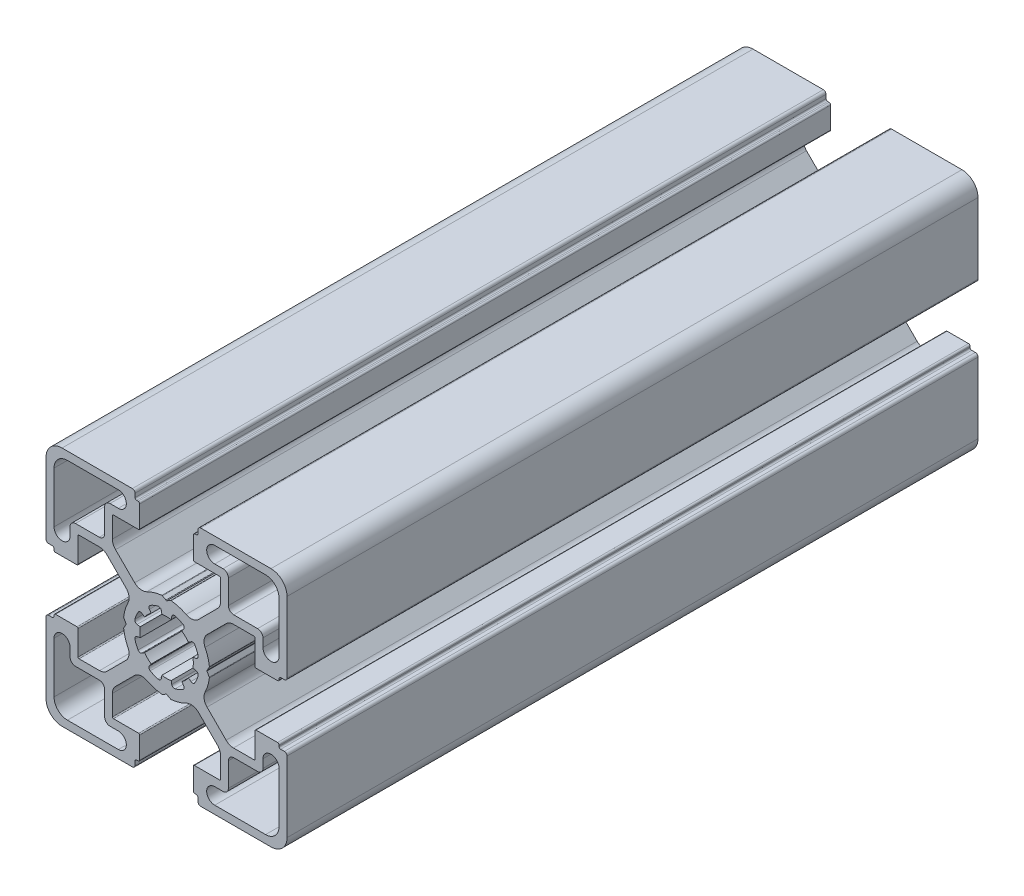
SolidWorks part; units mm, degrees
ref_plane "Front Plane" through (0, 0, 0) normal (0, 0, 1) x (1, 0, 0)
ref_plane "Top Plane" through (0, 0, 0) normal (0, 1, 0) x (1, 0, 0)
ref_plane "Right Plane" through (0, 0, 0) normal (1, 0, 0) x (0, 0, -1)
sketch "Sketch1" plane through (0, 0, 0) normal (0, 0, 1) x (1, 0, 0)
  line L0 (10.55, 18) -> (9, 18)
  line L1 (18.5, 21) -> (9, 21)
  line L2 (21, 9.0002) -> (21, 18.5)
  line L3 (18, 9.0002) -> (18, 10.55)
  line L4 (17, 11.55) -> (12.55, 11.55)
  line L5 (11.55, 12.55) -> (11.55, 17)
  line L6 (7.974, 0.7926) -> (7.5401, 0.0468)
  line L7 (-0.8674, 4.9242) -> (-0.9675, 5.4811)
  line L8 (-3.1913, 4.5626) -> (-2.864, 4.0985)
  line L9 (-4.0897, 2.8765) -> (-4.5668, 3.2082)
  line L10 (-5.4897, 0.9862) -> (-4.9205, 0.8878)
  line L11 (11.1298, 9.425) -> (7.5635, 5.8587)
  line L12 (16.3169, 9.9945) -> (12.5048, 9.9945)
  line L13 (16.5169, 5.2) -> (16.5169, 9.7945)
  line L14 (20.7196, 5) -> (16.7169, 5)
  line L15 (21.0196, 5.3) -> (21.0196, 5.5)
  line L16 (22, 5.8) -> (21.3196, 5.8)
  line L17 (22.5, 6.3) -> (22.5, 19.5)
  line L18 (19.5, 22.5) -> (6.3757, 22.5)
  line L19 (5.8757, 21.3) -> (5.8757, 22)
  line L20 (5.5757, 21) -> (5.3, 21)
  line L21 (5, 16.6668) -> (5, 20.7)
  line L22 (9.9054, 16.4668) -> (5.2, 16.4668)
  line L23 (10.1054, 12.4716) -> (10.1054, 16.2668)
  line L24 (5.9449, 7.4827) -> (9.5196, 11.0574)
  line L25 (0.1126, 7.6069) -> (0.7547, 7.9748)
  line L26 (5.4897, 0.9862) -> (4.9205, 0.8878)
  line L27 (4.0897, 2.8765) -> (4.5668, 3.2082)
  line L28 (3.1913, 4.5626) -> (2.864, 4.0985)
  line L29 (0.8674, 4.9242) -> (0.9675, 5.4811)
  line L30 (-10.55, -18) -> (-9, -18)
  line L31 (-18.5, -21) -> (-9, -21)
  line L32 (-21, -9.0002) -> (-21, -18.5)
  line L33 (-18, -9.0002) -> (-18, -10.55)
  line L34 (-17, -11.55) -> (-12.55, -11.55)
  line L35 (-11.55, -12.55) -> (-11.55, -17)
  line L36 (-7.974, -0.7926) -> (-7.5401, -0.0468)
  line L37 (-11.1298, -9.425) -> (-7.5635, -5.8587)
  line L38 (-16.3169, -9.9945) -> (-12.5048, -9.9945)
  line L39 (-16.5169, -5.2) -> (-16.5169, -9.7945)
  line L40 (-20.7196, -5) -> (-16.7169, -5)
  line L41 (-21.0196, -5.3) -> (-21.0196, -5.5)
  line L42 (-22, -5.8) -> (-21.3196, -5.8)
  line L43 (-22.5, -6.3) -> (-22.5, -19.5)
  line L44 (-19.5, -22.5) -> (-6.3757, -22.5)
  line L45 (-5.8757, -21.3) -> (-5.8757, -22)
  line L46 (-5.5757, -21) -> (-5.3, -21)
  line L47 (-5, -16.6668) -> (-5, -20.7)
  line L48 (-9.9054, -16.4668) -> (-5.2, -16.4668)
  line L49 (-10.1054, -12.4716) -> (-10.1054, -16.2668)
  line L50 (-5.9449, -7.4827) -> (-9.5196, -11.0574)
  line L51 (-0.1126, -7.6069) -> (-0.7547, -7.9748)
  line L52 (0.8674, -4.9242) -> (0.9675, -5.4811)
  line L53 (3.1913, -4.5626) -> (2.864, -4.0985)
  line L54 (4.0897, -2.8765) -> (4.5668, -3.2082)
  line L55 (5.4897, -0.9862) -> (4.9205, -0.8878)
  line L56 (0.1126, -7.6069) -> (0.7547, -7.9748)
  line L57 (5.9449, -7.4827) -> (9.5196, -11.0574)
  line L58 (10.1054, -12.4716) -> (10.1054, -16.2668)
  line L59 (9.9054, -16.4668) -> (5.2, -16.4668)
  line L60 (5, -16.6668) -> (5, -20.7)
  line L61 (5.5757, -21) -> (5.3, -21)
  line L62 (-0.1126, 7.6069) -> (-0.7547, 7.9748)
  line L63 (-5.9449, 7.4827) -> (-9.5196, 11.0574)
  line L64 (-10.1054, 12.4716) -> (-10.1054, 16.2668)
  line L65 (-9.9054, 16.4668) -> (-5.2, 16.4668)
  line L66 (-5, 16.6668) -> (-5, 20.7)
  line L67 (-5.5757, 21) -> (-5.3, 21)
  line L68 (-5.8757, 21.3) -> (-5.8757, 22)
  line L69 (-19.5, 22.5) -> (-6.3757, 22.5)
  line L70 (-22.5, 6.3) -> (-22.5, 19.5)
  line L71 (-22, 5.8) -> (-21.3196, 5.8)
  line L72 (-21.0196, 5.3) -> (-21.0196, 5.5)
  line L73 (-20.7196, 5) -> (-16.7169, 5)
  line L74 (-16.5169, 5.2) -> (-16.5169, 9.7945)
  line L75 (-16.3169, 9.9945) -> (-12.5048, 9.9945)
  line L76 (-11.1298, 9.425) -> (-7.5635, 5.8587)
  line L77 (-7.974, 0.7926) -> (-7.5401, 0.0468)
  line L78 (5.8757, -21.3) -> (5.8757, -22)
  line L79 (19.5, -22.5) -> (6.3757, -22.5)
  line L80 (22.5, -6.3) -> (22.5, -19.5)
  line L81 (22, -5.8) -> (21.3196, -5.8)
  line L82 (21.0196, -5.3) -> (21.0196, -5.5)
  line L83 (20.7196, -5) -> (16.7169, -5)
  line L84 (16.5169, -5.2) -> (16.5169, -9.7945)
  line L85 (16.3169, -9.9945) -> (12.5048, -9.9945)
  line L86 (11.1298, -9.425) -> (7.5635, -5.8587)
  line L87 (-5.4897, -0.9862) -> (-4.9205, -0.8878)
  line L88 (-4.0897, -2.8765) -> (-4.5668, -3.2082)
  line L89 (-3.1913, -4.5626) -> (-2.864, -4.0985)
  line L90 (-0.8674, -4.9242) -> (-0.9675, -5.4811)
  line L91 (7.974, -0.7926) -> (7.5401, -0.0468)
  line L92 (-11.55, 12.55) -> (-11.55, 17)
  line L93 (-17, 11.55) -> (-12.55, 11.55)
  line L94 (-18, 9.0002) -> (-18, 10.55)
  line L95 (-21, 9.0002) -> (-21, 18.5)
  line L96 (-18.5, 21) -> (-9, 21)
  line L97 (-10.55, 18) -> (-9, 18)
  line L98 (11.55, -12.55) -> (11.55, -17)
  line L99 (17, -11.55) -> (12.55, -11.55)
  line L100 (18, -9.0002) -> (18, -10.55)
  line L101 (21, -9.0002) -> (21, -18.5)
  line L102 (18.5, -21) -> (9, -21)
  line L103 (10.55, -18) -> (9, -18)
  line L104 (-33.3633, 0) -> (37.7265, 0) construction
  line L105 (0, 32.2957) -> (0, -36.0465) construction
  arc A0 (9, 18) -> (9, 21) centre (9, 19.5) cw
  arc A1 (18.5, 21) -> (21, 18.5) centre (18.5, 18.5) cw
  arc A2 (21, 9.0002) -> (18, 9.0002) centre (19.5, 9.0002) cw
  arc A3 (17, 11.55) -> (18, 10.55) centre (17, 10.55) cw
  arc A4 (12.55, 11.55) -> (11.55, 12.55) centre (12.55, 12.55) cw
  arc A5 (10.55, 18) -> (11.55, 17) centre (10.55, 17) cw
  arc A6 (7.5313, 0) -> (7.5401, 0.0468) centre (7.7309, -0.013) cw
  arc A7 (8, 0.9141) -> (7.974, 0.7926) centre (7.8011, 0.8932) cw
  arc A8 (7.2004, 3.6119) -> (8, 0.9141) centre (0.0496, 0.0249) cw
  arc A9 (7.2004, 3.6119) -> (7.5635, 5.8587) centre (8.9385, 4.4837) cw
  arc A10 (11.1298, 9.425) -> (12.5048, 9.9945) centre (12.5048, 8.05) cw
  arc A11 (16.3169, 9.9945) -> (16.5169, 9.7945) centre (16.3169, 9.7945) cw
  arc A12 (16.7169, 5) -> (16.5169, 5.2) centre (16.7169, 5.2) cw
  arc A13 (21.0196, 5.3) -> (20.7196, 5) centre (20.7196, 5.3) cw
  arc A14 (0.8674, 4.9242) -> (-0.8674, 4.9242) centre (0, 0) ccw
  arc A15 (-0.9675, 5.4811) -> (-1.5951, 5.8941) centre (-1.4627, 5.4119) ccw
  arc A16 (-1.5951, 5.8941) -> (-3.0444, 5.2994) centre (-0.0235, 0) ccw
  arc A17 (-3.0444, 5.2994) -> (-3.1913, 4.5626) centre (-2.7943, 4.8665) ccw
  arc A18 (-2.864, 4.0985) -> (-4.0897, 2.8765) centre (0, 0) ccw
  arc A19 (-4.5668, 3.2082) -> (-5.3025, 3.0565) centre (-4.868, 2.8091) ccw
  arc A20 (-5.3025, 3.0565) -> (-5.9068, 1.6112) centre (-0.0235, 0) ccw
  arc A21 (-5.9068, 1.6112) -> (-5.4897, 0.9862) centre (-5.4239, 1.4819) ccw
  arc A22 (-4.9205, 0.8878) -> (-5, 0) centre (0, 0) ccw
  arc A23 (21.0196, 5.5) -> (21.3196, 5.8) centre (21.3196, 5.5) cw
  arc A24 (22.5, 6.3) -> (22, 5.8) centre (22, 6.3) cw
  arc A25 (19.5, 22.5) -> (22.5, 19.5) centre (19.5, 19.5) cw
  arc A26 (5.8757, 22) -> (6.3757, 22.5) centre (6.3757, 22) cw
  arc A27 (5.8757, 21.3) -> (5.5757, 21) centre (5.5757, 21.3) cw
  arc A28 (5, 20.7) -> (5.3, 21) centre (5.3, 20.7) cw
  arc A29 (5.2, 16.4668) -> (5, 16.6668) centre (5.2, 16.6668) cw
  arc A30 (9.9054, 16.4668) -> (10.1054, 16.2668) centre (9.9054, 16.2668) cw
  arc A31 (10.1054, 12.4716) -> (9.5196, 11.0574) centre (8.1054, 12.4716) cw
  arc A32 (5.9449, 7.4827) -> (3.6665, 7.1733) centre (4.5855, 8.9496) cw
  arc A33 (0.8764, 8) -> (3.6665, 7.1733) centre (0.0235, 0) cw
  arc A34 (0.7547, 7.9748) -> (0.8764, 8) centre (0.8542, 7.8013) cw
  arc A35 (0.1126, 7.6069) -> (0, 7.531) centre (-0.0489, 7.7249) cw
  arc A36 (4.9205, 0.8878) -> (5, 0) centre (0, 0) cw
  arc A37 (5.9068, 1.6112) -> (5.4897, 0.9862) centre (5.4239, 1.4819) cw
  arc A38 (5.3025, 3.0565) -> (5.9068, 1.6112) centre (0.0235, 0) cw
  arc A39 (4.5668, 3.2082) -> (5.3025, 3.0565) centre (4.868, 2.8091) cw
  arc A40 (2.864, 4.0985) -> (4.0897, 2.8765) centre (0, 0) cw
  arc A41 (3.0444, 5.2994) -> (3.1913, 4.5626) centre (2.7943, 4.8665) cw
  arc A42 (1.5951, 5.8941) -> (3.0444, 5.2994) centre (0.0235, 0) cw
  arc A43 (0.9675, 5.4811) -> (1.5951, 5.8941) centre (1.4627, 5.4119) cw
  arc A44 (-9, -18) -> (-9, -21) centre (-9, -19.5) cw
  arc A45 (-18.5, -21) -> (-21, -18.5) centre (-18.5, -18.5) cw
  arc A46 (-21, -9.0002) -> (-18, -9.0002) centre (-19.5, -9.0002) cw
  arc A47 (-17, -11.55) -> (-18, -10.55) centre (-17, -10.55) cw
  arc A48 (-12.55, -11.55) -> (-11.55, -12.55) centre (-12.55, -12.55) cw
  arc A49 (-10.55, -18) -> (-11.55, -17) centre (-10.55, -17) cw
  arc A50 (-7.5313, 0) -> (-7.5401, -0.0468) centre (-7.7309, 0.013) cw
  arc A51 (-8, -0.9141) -> (-7.974, -0.7926) centre (-7.8011, -0.8932) cw
  arc A52 (-7.2004, -3.6119) -> (-8, -0.9141) centre (-0.0496, -0.0249) cw
  arc A53 (-7.2004, -3.6119) -> (-7.5635, -5.8587) centre (-8.9385, -4.4837) cw
  arc A54 (-11.1298, -9.425) -> (-12.5048, -9.9945) centre (-12.5048, -8.05) cw
  arc A55 (-16.3169, -9.9945) -> (-16.5169, -9.7945) centre (-16.3169, -9.7945) cw
  arc A56 (-16.7169, -5) -> (-16.5169, -5.2) centre (-16.7169, -5.2) cw
  arc A57 (-21.0196, -5.3) -> (-20.7196, -5) centre (-20.7196, -5.3) cw
  arc A58 (-21.0196, -5.5) -> (-21.3196, -5.8) centre (-21.3196, -5.5) cw
  arc A59 (-22.5, -6.3) -> (-22, -5.8) centre (-22, -6.3) cw
  arc A60 (-19.5, -22.5) -> (-22.5, -19.5) centre (-19.5, -19.5) cw
  arc A61 (-5.8757, -22) -> (-6.3757, -22.5) centre (-6.3757, -22) cw
  arc A62 (-5.8757, -21.3) -> (-5.5757, -21) centre (-5.5757, -21.3) cw
  arc A63 (-5, -20.7) -> (-5.3, -21) centre (-5.3, -20.7) cw
  arc A64 (-5.2, -16.4668) -> (-5, -16.6668) centre (-5.2, -16.6668) cw
  arc A65 (-9.9054, -16.4668) -> (-10.1054, -16.2668) centre (-9.9054, -16.2668) cw
  arc A66 (-10.1054, -12.4716) -> (-9.5196, -11.0574) centre (-8.1054, -12.4716) cw
  arc A67 (-5.9449, -7.4827) -> (-3.6665, -7.1733) centre (-4.5855, -8.9496) cw
  arc A68 (-0.8764, -8) -> (-3.6665, -7.1733) centre (-0.0235, 0) cw
  arc A69 (-0.7547, -7.9748) -> (-0.8764, -8) centre (-0.8542, -7.8013) cw
  arc A70 (-0.1126, -7.6069) -> (0, -7.531) centre (0.0489, -7.7249) cw
  arc A71 (0.9675, -5.4811) -> (1.5951, -5.8941) centre (1.4627, -5.4119) ccw
  arc A72 (1.5951, -5.8941) -> (3.0444, -5.2994) centre (0.0235, 0) ccw
  arc A73 (3.0444, -5.2994) -> (3.1913, -4.5626) centre (2.7943, -4.8665) ccw
  arc A74 (2.864, -4.0985) -> (4.0897, -2.8765) centre (0, 0) ccw
  arc A75 (4.5668, -3.2082) -> (5.3025, -3.0565) centre (4.868, -2.8091) ccw
  arc A76 (5.3025, -3.0565) -> (5.9068, -1.6112) centre (0.0235, 0) ccw
  arc A77 (5.9068, -1.6112) -> (5.4897, -0.9862) centre (5.4239, -1.4819) ccw
  arc A78 (4.9205, -0.8878) -> (5, 0) centre (0, 0) ccw
  arc A79 (0.1126, -7.6069) -> (0, -7.531) centre (-0.0489, -7.7249) ccw
  arc A80 (0.7547, -7.9748) -> (0.8764, -8) centre (0.8542, -7.8013) ccw
  arc A81 (0.8764, -8) -> (3.6665, -7.1733) centre (0.0235, 0) ccw
  arc A82 (5.9449, -7.4827) -> (3.6665, -7.1733) centre (4.5855, -8.9496) ccw
  arc A83 (10.1054, -12.4716) -> (9.5196, -11.0574) centre (8.1054, -12.4716) ccw
  arc A84 (9.9054, -16.4668) -> (10.1054, -16.2668) centre (9.9054, -16.2668) ccw
  arc A85 (5.2, -16.4668) -> (5, -16.6668) centre (5.2, -16.6668) ccw
  arc A86 (5, -20.7) -> (5.3, -21) centre (5.3, -20.7) ccw
  arc A87 (5.8757, -21.3) -> (5.5757, -21) centre (5.5757, -21.3) ccw
  arc A88 (-0.1126, 7.6069) -> (0, 7.531) centre (0.0489, 7.7249) ccw
  arc A89 (-0.7547, 7.9748) -> (-0.8764, 8) centre (-0.8542, 7.8013) ccw
  arc A90 (-0.8764, 8) -> (-3.6665, 7.1733) centre (-0.0235, 0) ccw
  arc A91 (-5.9449, 7.4827) -> (-3.6665, 7.1733) centre (-4.5855, 8.9496) ccw
  arc A92 (-10.1054, 12.4716) -> (-9.5196, 11.0574) centre (-8.1054, 12.4716) ccw
  arc A93 (-9.9054, 16.4668) -> (-10.1054, 16.2668) centre (-9.9054, 16.2668) ccw
  arc A94 (-5.2, 16.4668) -> (-5, 16.6668) centre (-5.2, 16.6668) ccw
  arc A95 (-5, 20.7) -> (-5.3, 21) centre (-5.3, 20.7) ccw
  arc A96 (-5.8757, 21.3) -> (-5.5757, 21) centre (-5.5757, 21.3) ccw
  arc A97 (-5.8757, 22) -> (-6.3757, 22.5) centre (-6.3757, 22) ccw
  arc A98 (-19.5, 22.5) -> (-22.5, 19.5) centre (-19.5, 19.5) ccw
  arc A99 (-22.5, 6.3) -> (-22, 5.8) centre (-22, 6.3) ccw
  arc A100 (-21.0196, 5.5) -> (-21.3196, 5.8) centre (-21.3196, 5.5) ccw
  arc A101 (-21.0196, 5.3) -> (-20.7196, 5) centre (-20.7196, 5.3) ccw
  arc A102 (-16.7169, 5) -> (-16.5169, 5.2) centre (-16.7169, 5.2) ccw
  arc A103 (-16.3169, 9.9945) -> (-16.5169, 9.7945) centre (-16.3169, 9.7945) ccw
  arc A104 (-11.1298, 9.425) -> (-12.5048, 9.9945) centre (-12.5048, 8.05) ccw
  arc A105 (-7.2004, 3.6119) -> (-7.5635, 5.8587) centre (-8.9385, 4.4837) ccw
  arc A106 (-7.2004, 3.6119) -> (-8, 0.9141) centre (-0.0496, 0.0249) ccw
  arc A107 (-8, 0.9141) -> (-7.974, 0.7926) centre (-7.8011, 0.8932) ccw
  arc A108 (-7.5313, 0) -> (-7.5401, 0.0468) centre (-7.7309, -0.013) ccw
  arc A109 (5.8757, -22) -> (6.3757, -22.5) centre (6.3757, -22) ccw
  arc A110 (19.5, -22.5) -> (22.5, -19.5) centre (19.5, -19.5) ccw
  arc A111 (22.5, -6.3) -> (22, -5.8) centre (22, -6.3) ccw
  arc A112 (21.0196, -5.5) -> (21.3196, -5.8) centre (21.3196, -5.5) ccw
  arc A113 (-4.9205, -0.8878) -> (-5, 0) centre (0, 0) cw
  arc A114 (-5.9068, -1.6112) -> (-5.4897, -0.9862) centre (-5.4239, -1.4819) cw
  arc A115 (-5.3025, -3.0565) -> (-5.9068, -1.6112) centre (-0.0235, 0) cw
  arc A116 (-4.5668, -3.2082) -> (-5.3025, -3.0565) centre (-4.868, -2.8091) cw
  arc A117 (-2.864, -4.0985) -> (-4.0897, -2.8765) centre (0, 0) cw
  arc A118 (-3.0444, -5.2994) -> (-3.1913, -4.5626) centre (-2.7943, -4.8665) cw
  arc A119 (-1.5951, -5.8941) -> (-3.0444, -5.2994) centre (-0.0235, 0) cw
  arc A120 (-0.9675, -5.4811) -> (-1.5951, -5.8941) centre (-1.4627, -5.4119) cw
  arc A121 (0.8674, -4.9242) -> (-0.8674, -4.9242) centre (0, 0) cw
  arc A122 (21.0196, -5.3) -> (20.7196, -5) centre (20.7196, -5.3) ccw
  arc A123 (16.7169, -5) -> (16.5169, -5.2) centre (16.7169, -5.2) ccw
  arc A124 (-10.55, 18) -> (-11.55, 17) centre (-10.55, 17) ccw
  arc A125 (-12.55, 11.55) -> (-11.55, 12.55) centre (-12.55, 12.55) ccw
  arc A126 (-17, 11.55) -> (-18, 10.55) centre (-17, 10.55) ccw
  arc A127 (-21, 9.0002) -> (-18, 9.0002) centre (-19.5, 9.0002) ccw
  arc A128 (-18.5, 21) -> (-21, 18.5) centre (-18.5, 18.5) ccw
  arc A129 (-9, 18) -> (-9, 21) centre (-9, 19.5) ccw
  arc A130 (16.3169, -9.9945) -> (16.5169, -9.7945) centre (16.3169, -9.7945) ccw
  arc A131 (11.1298, -9.425) -> (12.5048, -9.9945) centre (12.5048, -8.05) ccw
  arc A132 (7.2004, -3.6119) -> (7.5635, -5.8587) centre (8.9385, -4.4837) ccw
  arc A133 (7.2004, -3.6119) -> (8, -0.9141) centre (0.0496, -0.0249) ccw
  arc A134 (8, -0.9141) -> (7.974, -0.7926) centre (7.8011, -0.8932) ccw
  arc A135 (7.5313, 0) -> (7.5401, -0.0468) centre (7.7309, 0.013) ccw
  arc A136 (10.55, -18) -> (11.55, -17) centre (10.55, -17) ccw
  arc A137 (12.55, -11.55) -> (11.55, -12.55) centre (12.55, -12.55) ccw
  arc A138 (17, -11.55) -> (18, -10.55) centre (17, -10.55) ccw
  arc A139 (21, -9.0002) -> (18, -9.0002) centre (19.5, -9.0002) ccw
  arc A140 (18.5, -21) -> (21, -18.5) centre (18.5, -18.5) ccw
  arc A141 (9, -18) -> (9, -21) centre (9, -19.5) ccw
  dimension "D6" = 12.2
  dimension "D8" = 10
  dimension "D1" = 10
  dimension "D2" = 45
  dimension "D3" = 45
  dimension "D4" = 10
  dimension "D5" = 14.5
  dimension "D7" = 22.5
extrude "Base-Extrude" add sketch "Sketch1" against normal blind 129
